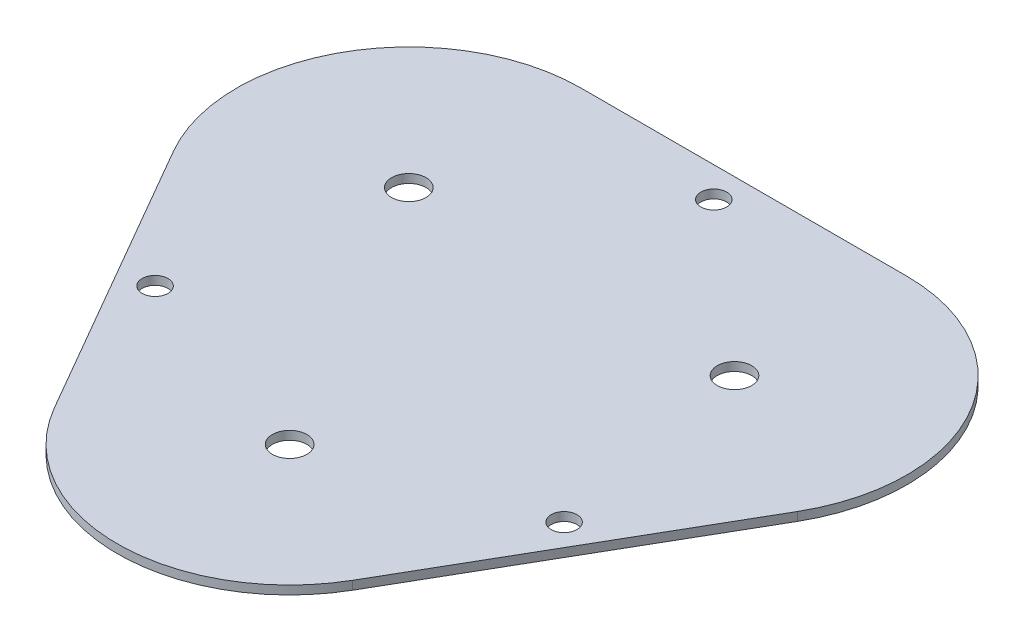
SolidWorks part; units mm, degrees
ref_plane "Front Plane" through (0, 0, 0) normal (0, 0, 1) x (1, 0, 0)
ref_plane "Top Plane" through (0, 0, 0) normal (0, 1, 0) x (1, 0, 0)
ref_plane "Right Plane" through (0, 0, 0) normal (1, 0, 0) x (0, 0, -1)
sketch "Sketch1" plane through (0, 0, 0) normal (0, 1, 0) x (1, 0, 0)
  line L0 (-18.9035, 10.9139) -> (18.9035, 10.9139) construction
  line L1 (-18.9035, 10.9139) -> (0, -21.8279) construction
  line L2 (36.224, 0.9139) -> (17.3205, -31.8279)
  line L3 (-36.224, 0.9139) -> (-17.3205, -31.8279)
  line L4 (-18.9035, 30.9139) -> (18.9035, 30.9139)
  line L5 (18.9035, 10.9139) -> (-49.174, -28.3906) construction
  line L6 (0, -21.8279) -> (0, 33.8455) construction
  line L7 (18.9035, 10.9139) -> (0, -21.8279) construction
  line L8 (-18.9035, 10.9139) -> (24.2933, -14.0257) construction
  circle A0 centre (0, 0) radius 21.8279 construction
  circle A1 centre (-18.9035, 10.9139) radius 2
  circle A2 centre (18.9035, 10.9139) radius 2
  circle A3 centre (0, -21.8279) radius 2
  arc A4 (-18.9035, 30.9139) -> (-36.224, 0.9139) centre (-18.9035, 10.9139) ccw
  circle A5 centre (-23.7412, -13.707) radius 1.5
  arc A6 (-17.3205, -31.8279) -> (17.3205, -31.8279) centre (0, -21.8279) ccw
  circle A7 centre (23.7412, -13.707) radius 1.5
  circle A8 centre (0, 27.4139) radius 1.5
  arc A9 (36.224, 0.9139) -> (18.9035, 30.9139) centre (18.9035, 10.9139) ccw
  dimension "D4" = 4
  dimension "D5" = 4
  dimension "D6" = 4
  dimension "D7" = 40
  dimension "D9" = 40
  dimension "D8" = 3
  dimension "D11" = 3
  dimension "D13" = 3
  dimension "D1" = 37.807
  dimension "D2" = 37.807
  dimension "D3" = 37.807
  dimension "D10" = 3.5
  dimension "D12" = 3.5
  dimension "D14" = 3.5
extrude "Boss-Extrude1" add sketch "Sketch1" along normal blind 1
sketch "Sketch2" plane through (0, 0, 0) normal (0, -1, 0) x (1, 0, 0)
  line L0 (-2.5, 1.5) -> (2.5, 1.5)
  line L1 (2.5, 1.5) -> (2.5, -1.5)
  line L2 (2.5, -1.5) -> (-2.5, -1.5)
  line L3 (-2.5, -1.5) -> (-2.5, 1.5)
  point P5 (2.5, 0)
  dimension "D1" = 2.5
  dimension "D2" = 3
  dimension "D3" = 1.5
  dimension "D4" = 5
extrude "Boss-Extrude2" add sketch "Sketch2" along normal blind 4 contours L0 L1 L2 L3
equation "\"thread_dist\"= 3.5"
equation "\"thread_diameter\"= 3"
equation "\"D13@Sketch1\"=\"thread_diameter\""
equation "\"D14@Sketch1\"=\"thread_dist\""
equation "\"D11@Sketch1\"=\"thread_diameter\""
equation "\"D12@Sketch1\"=\"thread_dist\""
equation "\"D8@Sketch1\"=\"thread_diameter\""
equation "\"D10@Sketch1\"=\"thread_dist\""
